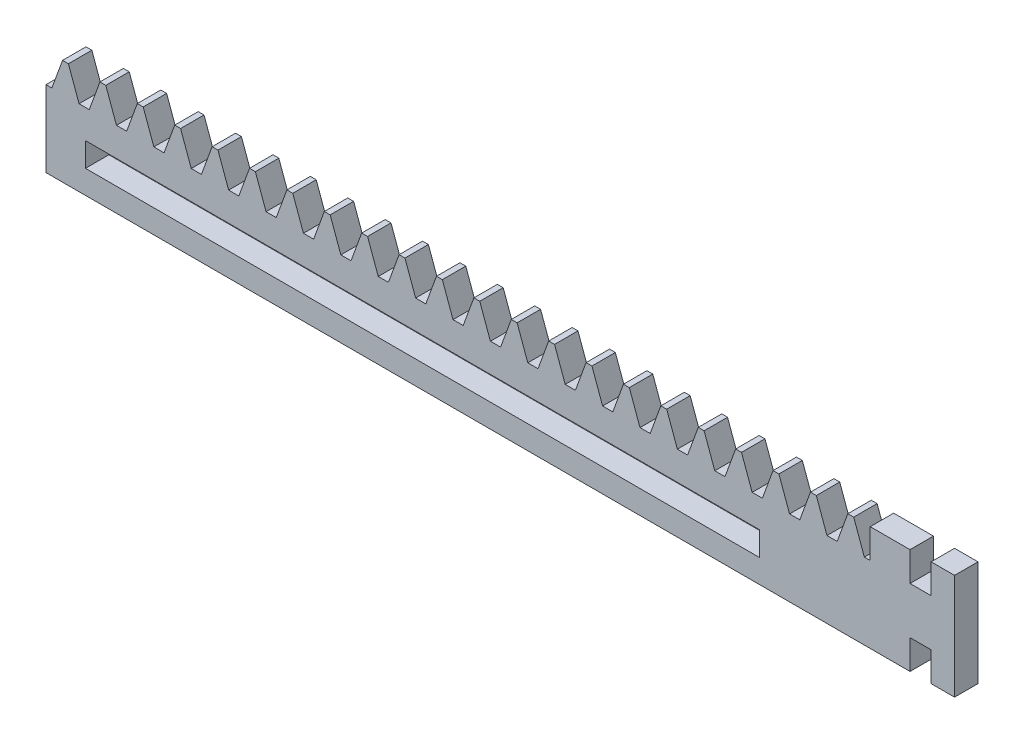
SolidWorks part; units mm, degrees
ref_plane "Ebene vorne" through (0, 0, 0) normal (0, 0, 1) x (1, 0, 0)
ref_plane "Ebene oben" through (0, 0, 0) normal (0, 1, 0) x (1, 0, 0)
ref_plane "Ebene rechts" through (0, 0, 0) normal (1, 0, 0) x (0, 0, -1)
sketch "Skizze1" plane through (0, 0, 0) normal (0, 0, 1) x (1, 0, 0)
  line L5 (0, 0) -> (155, 0)
  line L6 (0, 0) -> (0, 18)
  line L7 (0, 18) -> (155, 18)
  line L8 (155, 0) -> (155, 18)
  dimension "D1" = 18
  dimension "D2" = 155
extrude "Aufsatz-Linear austragen1" add sketch "Skizze1" along normal blind 4
sketch "Skizze2" plane through (0, 0, 4) normal (0, 0, 1) x (1, 0, 0)
  line L0 (0, 13) -> (1, 13)
  line L1 (0, 18) -> (0, 0) construction
  line L2 (1, 13) -> (2.8199, 18)
  line L3 (155, 18) -> (0, 18) construction
  line L4 (155, 18) -> (0, 18) construction
  line L7 (3.8199, 18) -> (5.6397, 13)
  line L8 (5.6397, 13) -> (6.6397, 13)
  line L14 (6.6397, 13) -> (6.6397, 18)
  line L15 (6.6397, 18) -> (3.8199, 18)
  line L16 (0, 18) -> (0, 13)
  line L17 (2.8199, 18) -> (0, 18)
  dimension "D1" = 5
  dimension "D2" = 110
  dimension "D3" = 1
  dimension "D6" = 1
extrude "Schnitt-Linear austragen1" cut sketch "Skizze2" against normal up to next (4 mm away)
pattern_linear "Lineares Muster1" count 22 spacing 6.3797 along (1, 0, 0) of "Schnitt-Linear austragen1"
sketch "Skizze3" plane through (0, 0, 4) normal (0, 0, 1) x (1, 0, 0)
  line L0 (0, 0) -> (155, 0) construction
  line L1 (6.7276, 4) -> (121.7276, 4)
  line L2 (6.7276, 4) -> (6.7276, 8.1)
  line L3 (6.7276, 8.1) -> (121.7276, 8.1)
  line L4 (121.7276, 4) -> (121.7276, 8.1)
  line L5 (0, 13) -> (0, 0) construction
  point P8 (6.7276, 6.05)
  dimension "D1" = 4.1
  dimension "D2" = 115
  dimension "D3" = 4
  dimension "D4" = 6.7276
extrude "Schnitt-Linear austragen2" cut sketch "Skizze3" against normal up to next
sketch "Skizze4" plane through (0, 0, 4) normal (0, 0, 1) x (1, 0, 0)
  line L6 (155, 18) -> (140.6125, 18) construction
  line L7 (151, 18) -> (147.4, 18)
  line L8 (151, 18) -> (151, 13)
  line L9 (151, 13) -> (147.4, 13)
  line L10 (147.4, 18) -> (147.4, 13)
  line L11 (0, 0) -> (155, 0) construction
  line L12 (147.4, 0) -> (151, 0)
  line L13 (147.4, 0) -> (147.4, 5)
  line L14 (147.4, 5) -> (151, 5)
  line L15 (151, 0) -> (151, 5)
  line L16 (171.9025, 9) -> (109.7493, 9) construction
  line L17 (155, 0) -> (155, 18) construction
  dimension "D1" = 8
  dimension "D2" = 3.6
  dimension "D3" = 4
extrude "Schnitt-Linear austragen3" cut sketch "Skizze4" against normal up to next
